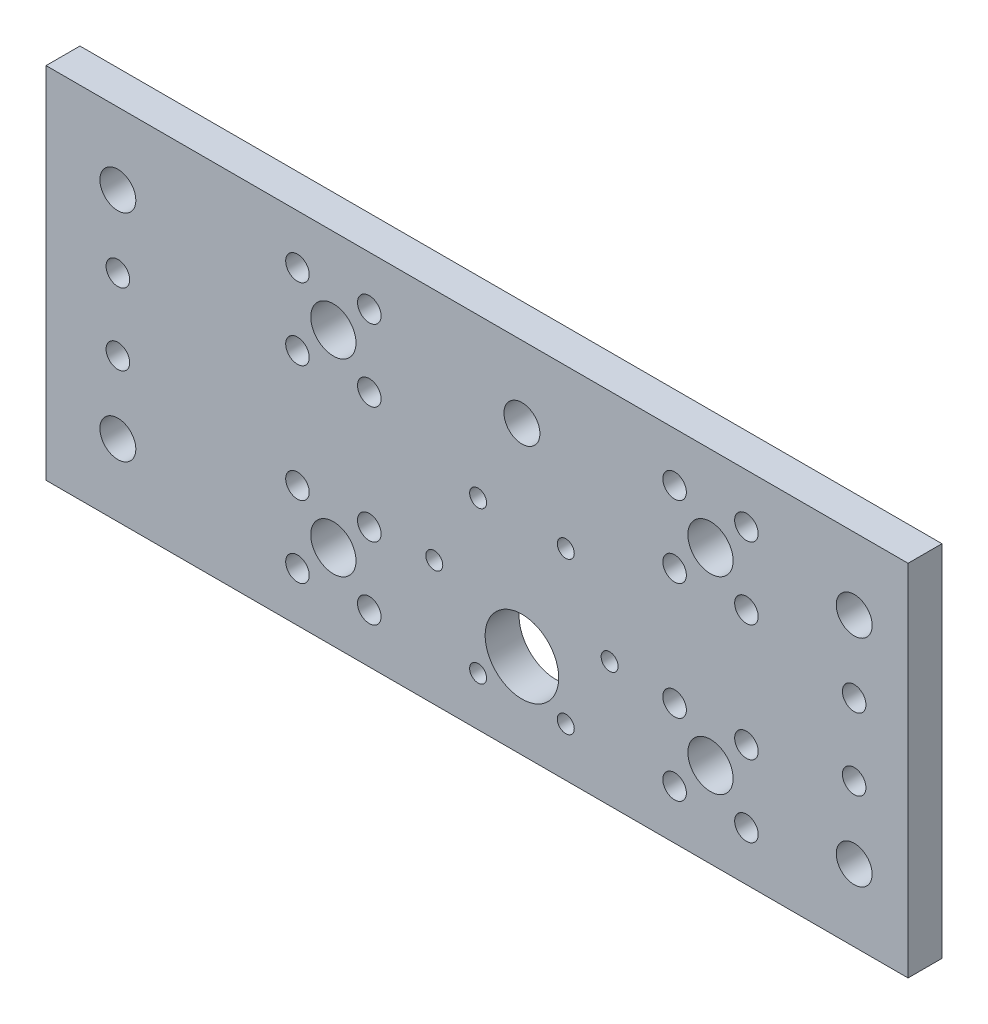
SolidWorks part; units mm, degrees
ref_plane "Front Plane" through (0, 0, 0) normal (0, 0, 1) x (1, 0, 0)
ref_plane "Top Plane" through (0, 0, 0) normal (0, 1, 0) x (1, 0, 0)
ref_plane "Right Plane" through (0, 0, 0) normal (1, 0, 0) x (0, 0, -1)
sketch "Sketch1" plane through (0, 0, 0) normal (0, 0, 1) x (1, 0, 0)
  line L0 (12.7, 63.5) -> (12.7, 0) construction
  line L1 (0, 0) -> (152.4, 0)
  line L2 (0, 0) -> (0, 63.5)
  line L3 (0, 63.5) -> (152.4, 63.5)
  line L4 (152.4, 0) -> (152.4, 63.5)
  line L5 (68.6375, 22.0749) -> (84.1375, 22.0749) construction
  line L6 (84.1375, 22.0749) -> (93.3875, 38.0964) construction
  line L7 (84.1375, 22.0749) -> (93.3875, 6.0534) construction
  line L8 (84.1375, 22.0749) -> (99.6375, 22.0749) construction
  line L9 (142.875, 63.5) -> (142.875, 0) construction
  line L10 (0, 31.75) -> (152.4, 31.75) construction
  circle A0 centre (84.1375, 15.0749) radius 6.5
  circle A1 centre (84.1375, 22.0749) radius 18.5 construction
  circle A2 centre (68.6375, 22.0749) radius 1.5
  circle A3 centre (99.6375, 22.0749) radius 1.5
  circle A4 centre (91.8875, 8.6515) radius 1.5
  circle A5 centre (76.3875, 8.6515) radius 1.5
  circle A6 centre (76.3875, 35.4983) radius 1.5
  circle A7 centre (91.8875, 35.4983) radius 1.5
  circle A8 centre (84.1375, 22.0749) radius 15.5 construction
  circle A9 centre (50.8, 48.4251) radius 4
  circle A10 centre (12.7, 50.8) radius 3.175
  circle A11 centre (12.7, 12.7) radius 3.175
  circle A12 centre (117.475, 48.4251) radius 4
  circle A13 centre (117.475, 15.0749) radius 4
  circle A14 centre (50.8, 15.0749) radius 4
  circle A15 centre (44.45, 21.4249) radius 2.0828
  circle A16 centre (44.45, 8.7249) radius 2.0828
  circle A17 centre (57.15, 8.7249) radius 2.0828
  circle A18 centre (57.15, 21.4249) radius 2.0828
  circle A19 centre (44.45, 54.7751) radius 2.0828
  circle A20 centre (44.45, 42.0751) radius 2.0828
  circle A21 centre (57.15, 42.0751) radius 2.0828
  circle A22 centre (57.15, 54.7751) radius 2.0828
  circle A23 centre (111.125, 54.7751) radius 2.0828
  circle A24 centre (111.125, 42.0751) radius 2.0828
  circle A25 centre (123.825, 42.0751) radius 2.0828
  circle A26 centre (123.825, 54.7751) radius 2.0828
  circle A27 centre (142.875, 50.8) radius 3.175
  circle A28 centre (142.875, 12.7) radius 3.175
  circle A29 centre (84.1375, 50.8) radius 3.175
  circle A30 centre (12.7, 38.1) radius 2.0828
  circle A31 centre (111.125, 21.4249) radius 2.0828
  circle A32 centre (111.125, 8.7249) radius 2.0828
  circle A33 centre (123.825, 8.7249) radius 2.0828
  circle A34 centre (123.825, 21.4249) radius 2.0828
  circle A35 centre (12.7, 25.4) radius 2.0828
  circle A36 centre (142.875, 38.1) radius 2.0828
  circle A37 centre (142.875, 25.4) radius 2.0828
  dimension "D3" = 13
  dimension "D4" = 37
  dimension "D7" = 3
  dimension "D10" = 8
  dimension "D12" = 15.5
  dimension "D15" = 7.75
  dimension "D8" = 31
  dimension "D14" = 31
  dimension "D17" = 66.675
  dimension "D20" = 4.1656
  dimension "D25" = 6.35
  dimension "D26" = 12.7
  dimension "D27" = 12.7
  dimension "D33" = 4.1656
  dimension "D34" = 4.1656
  dimension "D39" = 4.1656
  dimension "D45" = 6.35
  dimension "D48" = 6.35
  dimension "D49" = 4.1656
  dimension "D50" = 12.7
  dimension "D52" = 4.1656
  dimension "D53" = 12.7
  dimension "D1" = 152.4
  dimension "D5" = 7
  dimension "D6" = 33.3375
  dimension "D9" = 120
  dimension "D11" = 60
  dimension "D13" = 63.5
  dimension "D16" = 33.3502
  dimension "D18" = 6.35
  dimension "D19" = 33.3502
  dimension "D21" = 12.7
  dimension "D22" = 12.7
  dimension "D23" = 12.7
  dimension "D24" = 6.35
  dimension "D28" = 50.8
  dimension "D29" = 12.7
  dimension "D30" = 6.35
  dimension "D31" = 12.7
  dimension "D32" = 6.35
  dimension "D35" = 12.7
  dimension "D36" = 6.35
  dimension "D37" = 6.35
  dimension "D38" = 12.7
  dimension "D40" = 12.7
  dimension "D41" = 12.7
  dimension "D42" = 6.35
  dimension "D43" = 6.35
  dimension "D44" = 25.4
  dimension "D46" = 12.7
  dimension "D47" = 12.7
  dimension "D51" = 6.35
  dimension "D54" = 12.7
extrude "Boss-Extrude1" add sketch "Sketch1" along normal blind 5.9944
